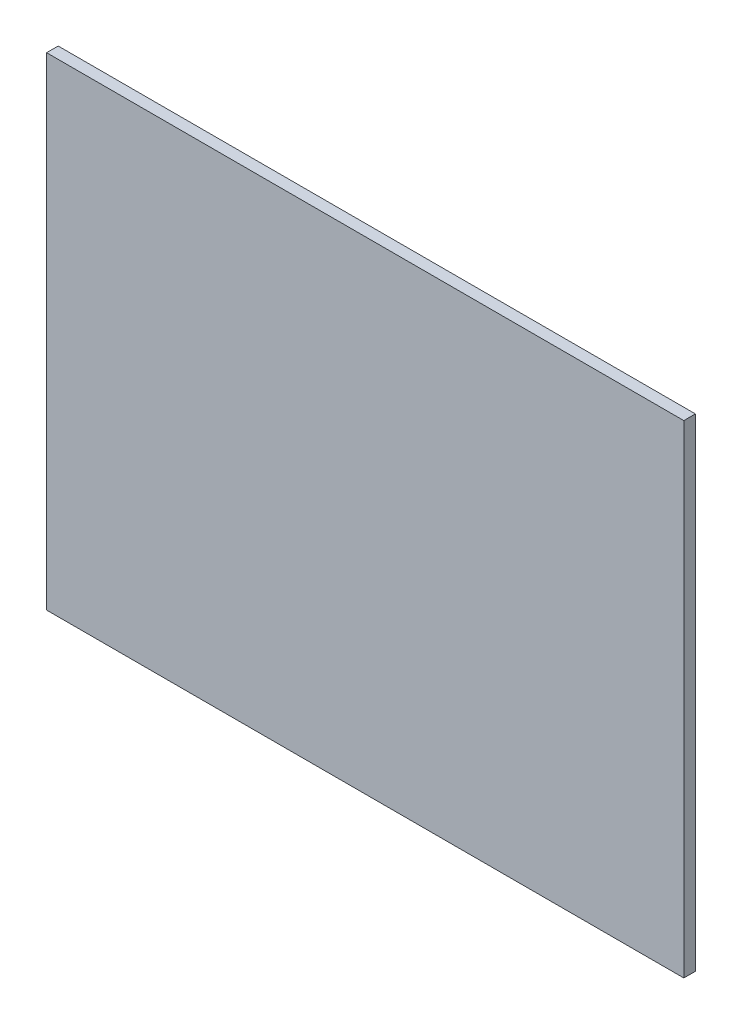
SolidWorks part; units mm, degrees
ref_plane "Plan de face" through (0, 0, 0) normal (0, 0, 1) x (1, 0, 0)
ref_plane "Plan de dessus" through (0, 0, 0) normal (0, 1, 0) x (1, 0, 0)
ref_plane "Plan de droite" through (0, 0, 0) normal (1, 0, 0) x (0, 0, -1)
sketch "Esquisse1" plane through (0, 0, 0) normal (0, 0, 1) x (1, 0, 0)
  line L1 (-129.2363, 131.7568) -> (200.7637, 131.7568)
  line L2 (-129.2363, 131.7568) -> (-129.2363, -118.2432)
  line L3 (-129.2363, -118.2432) -> (200.7637, -118.2432)
  line L4 (200.7637, 131.7568) -> (200.7637, -118.2432)
  dimension "D1" = 330
  dimension "D2" = 250
extrude "Boss.-Extru.1" add sketch "Esquisse1" along normal blind 6
